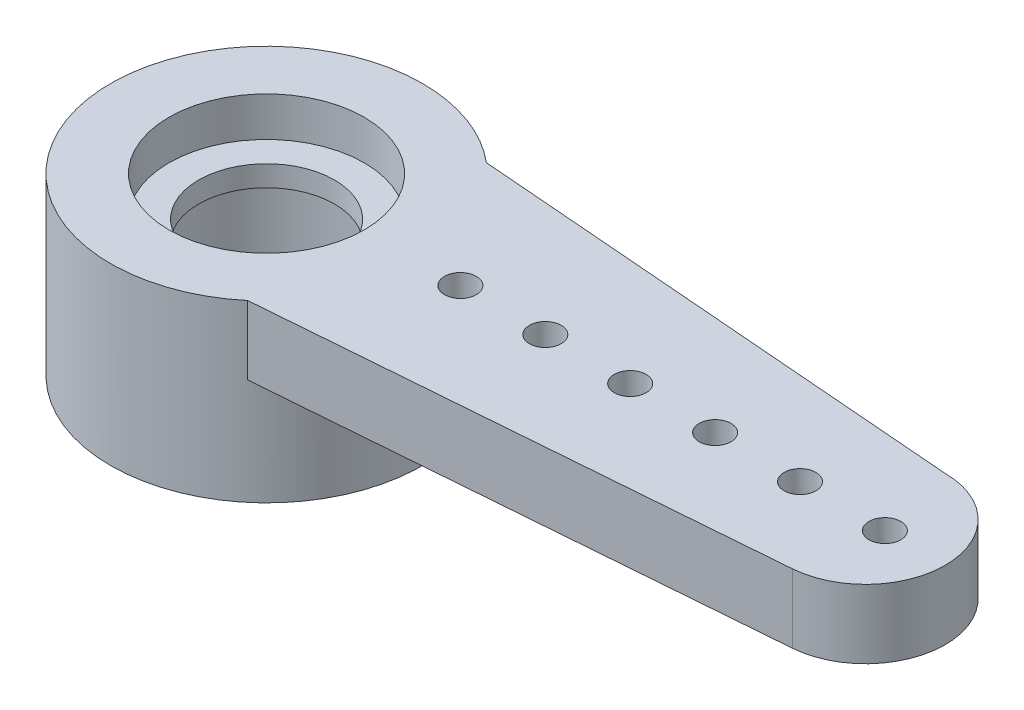
SolidWorks part; units mm, degrees
material "ABS"
ref_plane "Front Plane" through (0, 0, 0) normal (0, 0, 1) x (1, 0, 0)
ref_plane "Top Plane" through (0, 0, 0) normal (0, 1, 0) x (1, 0, 0)
ref_plane "Right Plane" through (0, 0, 0) normal (1, 0, 0) x (0, 0, -1)
sketch "Sketch1" plane through (0, 0, 0) normal (0, 1, 0) x (1, 0, 0)
  line L2 (-32.4126, 10.0098) -> (-18.3026, 10.0098) construction
  line L3 (-30.0457, 12.8211) -> (-18.3026, 11.8848)
  line L4 (-30.047, 7.1974) -> (-18.1543, 8.1406)
  arc A0 (-30.0457, 12.8211) -> (-30.047, 7.1974) centre (-32.4126, 10.0098) ccw
  arc A1 (-18.1543, 8.1406) -> (-18.3026, 11.8848) centre (-18.3026, 10.0098) ccw
  dimension "D1" = 14.11
extrude "Boss-Extrude1" add sketch "Sketch1" along normal blind 1.62
sketch "Sketch2" plane through (0, 0, 0) normal (0, -1, 0) x (1, 0, 0)
  circle A1 centre (-32.4126, -10.0098) radius 3.675
extrude "Boss-Extrude2" add sketch "Sketch2" along normal blind 2.5
sketch "Sketch3" plane through (0, -2.5, 0) normal (0, -1, 0) x (1, 0, 0)
  circle A0 centre (-32.4126, -10.0098) radius 1.6
  circle A1 centre (-32.4126, -10.0098) radius 2.3
extrude "Cut-Extrude1" cut sketch "Sketch3" against normal blind 2.7
sketch "Sketch4" plane through (0, -2.5, 0) normal (0, -1, 0) x (1, 0, 0)
  circle A0 centre (-32.4126, -10.0098) radius 1.6
extrude "Cut-Extrude2" cut sketch "Sketch4" against normal up to surface (4.12 mm away) up to face at (-25.1979, 1.62, -10.0291)
sketch "Sketch5" plane through (0, 1.62, 0) normal (0, 1, 0) x (1, 0, 0)
  circle A2 centre (-32.4126, 10.0098) radius 2.3
  circle A3 centre (-32.4126, 10.0098) radius 2.3
  dimension "D1" = 0.7
extrude "Cut-Extrude3" cut sketch "Sketch5" against normal blind 0.93
sketch "Sketch7" plane through (0, 0, 0) normal (0, -1, 0) x (1, 0, 0)
  line L0 (-18.3026, -10.0098) -> (-28.7376, -10.0089) construction
  arc A0 (-30.0457, -12.8211) -> (-30.047, -7.1974) centre (-32.4126, -10.0098) ccw construction
  circle A1 centre (-27.8463, -10.009) radius 0.375
  circle A2 centre (-25.8463, -10.009) radius 0.375
  circle A3 centre (-23.8463, -10.009) radius 0.375
  circle A4 centre (-21.8463, -10.009) radius 0.375
  circle A5 centre (-19.8463, -10.009) radius 0.375
  circle A6 centre (-17.8463, -10.009) radius 0.375
  circle A7 centre (-32.4126, -10.0098) radius 2.3 construction
  circle A8 centre (-32.4126, -10.0098) radius 2.3
  dimension "D1" = 6
  dimension "D2" = 14.5663
extrude "Cut-Extrude4" cut sketch "Sketch7" against normal up to surface (1.62 mm away) contours L0 A1 | L0 A2 | A2 L0 | A1 L0 | A3 L0 | L0 A3 | L0 A4 | A4 L0 | A5 L0 | L0 A5 | A6
